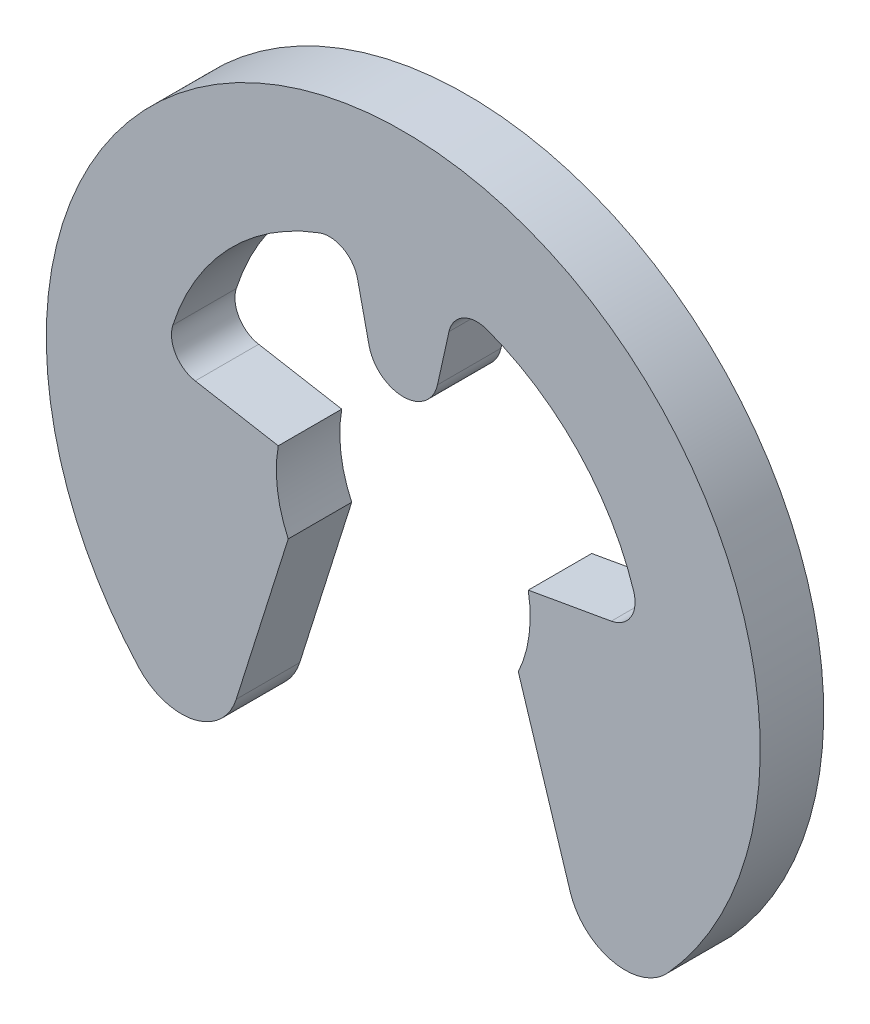
SolidWorks part; units mm, degrees
ref_plane "Plane1" through (0, 0, 0) normal (0, 0, 1) x (1, 0, 0)
ref_plane "Plane2" through (0, 0, 0) normal (0, 1, 0) x (1, 0, 0)
ref_plane "Plane3" through (0, 0, 0) normal (1, 0, 0) x (0, 0, -1)
sketch "BodySke" plane through (0, 0, 0) normal (0, 0, 1) x (1, 0, 0)
  line L0 (-0.7581, 0) -> (0.7581, 0) construction
  line L1 (0, 0) -> (0, 1.125) construction
  line L2 (0, 0) -> (0.1641, 0.7402) construction
  line L3 (0, 0) -> (1.0196, -0.4754) construction
  line L4 (0, 0) -> (-0.1641, 0.7402) construction
  line L5 (0, 0) -> (-1.0196, -0.4754) construction
  line L6 (0.3939, 0.0695) -> (0.6556, 0.1156)
  line L7 (-0.3939, 0.0695) -> (-0.6556, 0.1156)
  line L8 (0, 0) -> (1.1079, 0.1954) construction
  line L9 (0.3625, -0.169) -> (0.5263, -0.6884)
  line L10 (-0.3625, -0.169) -> (-0.5263, -0.6884)
  line L11 (0.1079, 0.4866) -> (0.1441, 0.65)
  line L12 (-0.1079, 0.4866) -> (-0.1441, 0.65)
  line L13 (0, 0) -> (-1.1079, 0.1954) construction
  circle A0 centre (0, 0) radius 0.4 construction
  arc A1 (0.7262, 0.2325) -> (0.2639, 0.7154) centre (0, 0) ccw
  arc A2 (0.8334, -0.7557) -> (-0.8334, -0.7557) centre (0, 0) ccw
  arc A3 (0.3625, -0.169) -> (0.3939, 0.0695) centre (0, 0) ccw
  arc A4 (-0.2639, 0.7154) -> (-0.7262, 0.2325) centre (0, 0) ccw
  arc A5 (0.6556, 0.1156) -> (0.7262, 0.2325) centre (0.6399, 0.2049) ccw
  arc A7 (0.2639, 0.7154) -> (0.1441, 0.65) centre (0.2326, 0.6303) ccw
  arc A8 (-0.3939, 0.0695) -> (-0.3625, -0.169) centre (0, 0) ccw
  arc A9 (-0.7262, 0.2325) -> (-0.6556, 0.1156) centre (-0.6399, 0.2049) ccw
  arc A10 (-0.1079, 0.4866) -> (0.1079, 0.4866) centre (0, 0.5105) ccw
  arc A11 (-0.1441, 0.65) -> (-0.2639, 0.7154) centre (-0.2326, 0.6303) ccw
  arc A12 (-0.8334, -0.7557) -> (-0.5263, -0.6884) centre (-0.6991, -0.6339) ccw
  arc A13 (0.5263, -0.6884) -> (0.8334, -0.7557) centre (0.6991, -0.6339) ccw
  dimension "D1" = 35
  dimension "GrooveDia" = 0.8
  dimension "OutsideDia" = 2.25
  dimension "D3" = 25
  dimension "TipRad" = 0.1812
  dimension "D2" = 160
  dimension "CavityDia" = 1.525
  dimension "CavityFilletRad" = 0.0906
  dimension "D4" = 35
extrude "Body" add sketch "BodySke" against normal blind 0.2
equation "' \"Thickness@Body\" = 0.2"
equation "' \"GrooveDia@BodySke\" = 0.8"
equation "' \"OutsideDia@BodySke\" = 2.25"
equation "' \"Thickness@Body\" = 2.5"
equation "' \"GrooveDia@BodySke\" = 30"
equation "' \"OutsideDia@BodySke\" = 52.6"
equation "\"CavityDia@BodySke\" = (\"OutsideDia@BodySke\"  + \"GrooveDia@BodySke\") / 2 "
equation "\"CavityFilletRad@BodySke\" =  (\"CavityDia@BodySke\" - \"GrooveDia@BodySke\") / 2 * 0.25"
equation "\"TipRad@BodySke\" = (\"OutsideDia@BodySke\"  - \"GrooveDia@BodySke\") / 2 * 0.25"
